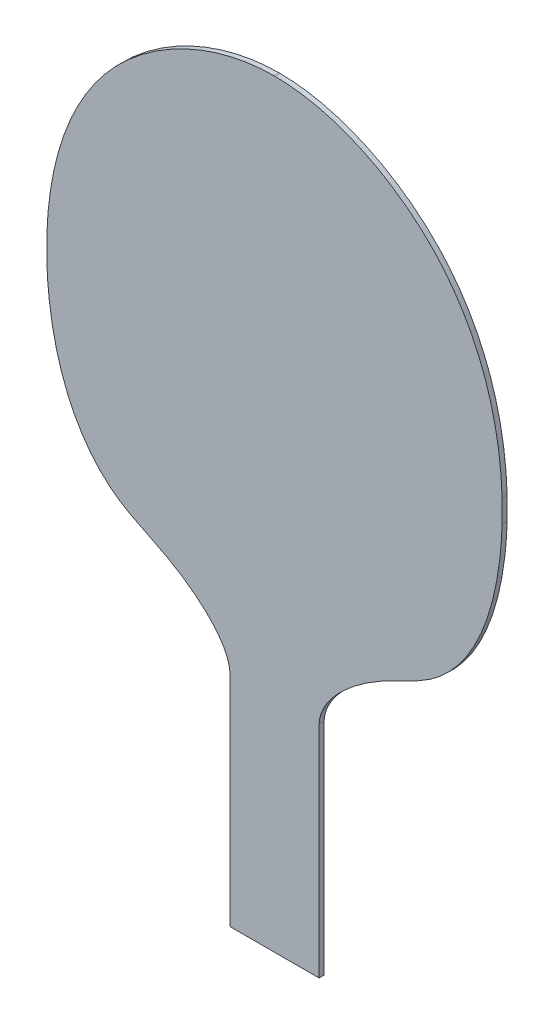
SolidWorks part; units mm, degrees
ref_plane "Front Plane" through (0, 0, 0) normal (0, 0, 1) x (1, 0, 0)
ref_plane "Top Plane" through (0, 0, 0) normal (0, 1, 0) x (1, 0, 0)
ref_plane "Right Plane" through (0, 0, 0) normal (1, 0, 0) x (0, 0, -1)
sketch "Sketch1" plane through (0, 0, 0) normal (0, 0, 1) x (1, 0, 0)
  line L0 (-24.1848, 127.6242) -> (160.1779, 127.6242) construction
  line L1 (90, 300) -> (90, 0) construction
  line L2 (0, 0) -> (180, 0)
  line L3 (0, 0) -> (0, 300)
  line L4 (0, 300) -> (180, 300)
  line L5 (180, 0) -> (180, 300)
  line L6 (72.3747, 0) -> (72.3747, 86.9999)
  line L7 (107.6253, 0) -> (107.6253, 86.9999)
  spline S0 degree 3 poles (72.3747, 86.9999) (71.9459, 95.9781) (52.5134, 113.8663) (31.1047, 121.0691) (7.1517, 142.8938) (-6.8857, 200.2363) (13.8242, 274.6667) (66.9865, 300.0409) (90, 300) knots 0 0 0 0 0.116861 0.211663 0.246387 0.4641 0.758219 1 1 1 1
  spline S1 degree 3 poles (107.6253, 86.9999) (108.0541, 95.9781) (127.4866, 113.8663) (148.8953, 121.0691) (172.8483, 142.8938) (186.8857, 200.2363) (166.1758, 274.6667) (113.0135, 300.0409) (90, 300) knots 0 0 0 0 0.116861 0.211663 0.246387 0.4641 0.758219 1 1 1 1
  dimension "D1" = 300
  dimension "D2" = 180
extrude "Boss-Extrude2" add sketch "Sketch1" along normal blind 2 contours L7 S1 L5 L4 S0 L3 L6 L2
